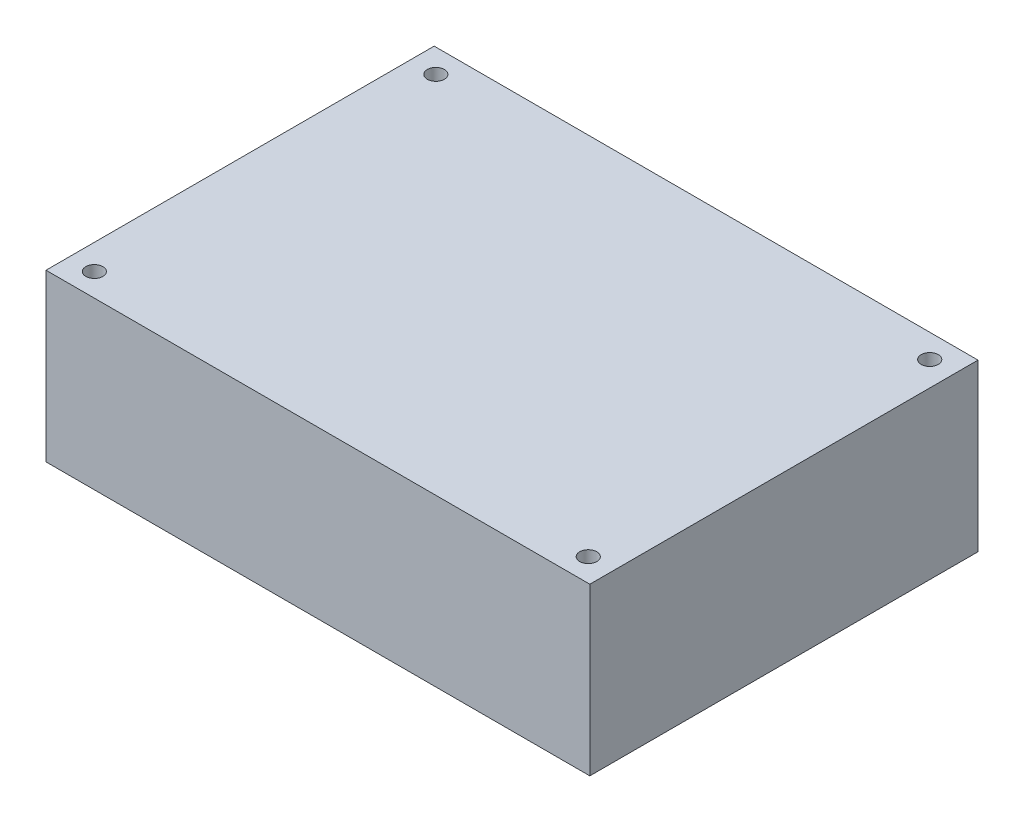
SolidWorks part; units mm, degrees
ref_plane "Front Plane" through (0, 0, 0) normal (0, 0, 1) x (1, 0, 0)
ref_plane "Top Plane" through (0, 0, 0) normal (0, 1, 0) x (1, 0, 0)
ref_plane "Right Plane" through (0, 0, 0) normal (1, 0, 0) x (0, 0, -1)
sketch "Sketch2" plane through (0, 0, 0) normal (0, 1, 0) x (1, 0, 0)
  line L0 (-35.052, 25.019) -> (35.052, -25.019) construction
  line L1 (-35.052, 25.019) -> (35.052, 25.019)
  line L2 (-35.052, 25.019) -> (-35.052, -25.019)
  line L3 (-35.052, -25.019) -> (35.052, -25.019)
  line L4 (35.052, 25.019) -> (35.052, -25.019)
  line L5 (35.052, 25.019) -> (-35.052, -25.019) construction
  point P4 (0, 0)
  point P5 (0, 0)
  dimension "D1" = 70.104
  dimension "D2" = 50.038
extrude "Boss-Extrude1" add sketch "Sketch2" along normal blind 21.3995
hole_wizard "M2 Clearance Hole1" positions "Sketch3" profile "Sketch4" hole size "M2" standard "ANSI Metric" end condition through all
sketch "Sketch3" plane through (0, 0, 0) normal (0, -1, 0) x (-1, 0, 0)
  point P0 (-31.877, 21.971)
  point P2 (-31.877, -22.0472)
  point P4 (31.7881, -22.0472)
  point P6 (31.7881, 21.971)
  point P12 (-31.877, 11.2785)
  point P17 (-31.877, 11.2785)
  point P22 (47.2396, 25.286)
  dimension "D1" = 63.6651
  dimension "D2" = 44.0182
  dimension "D3" = 44.0182
  dimension "D4" = 63.6651
  dimension "D5" = 31.877
  dimension "D6" = 21.971
sketch "Sketch4" plane through (31.877, 0, -21.971) normal (1, 0, 0) x (0, 0, -1)
  line L0 (0, 0) -> (0, 21.3995)
  line L1 (0, 21.3995) -> (1.1, 21.3995)
  line L2 (1.1, 21.3995) -> (1.1, 0)
  line L5 (1.1, 0) -> (0, 0)
  line L11 (0, -6.35) -> (0, 107.95) construction
  dimension "Thru Hole Dia." = 2.2
  dimension "Thru Hole Depth" = 21.3995
equation "\"board length\"= 2.7605in"
equation "\"board width\"= 1.9745in"
equation "\"board thickness\"= 0.0645in"
